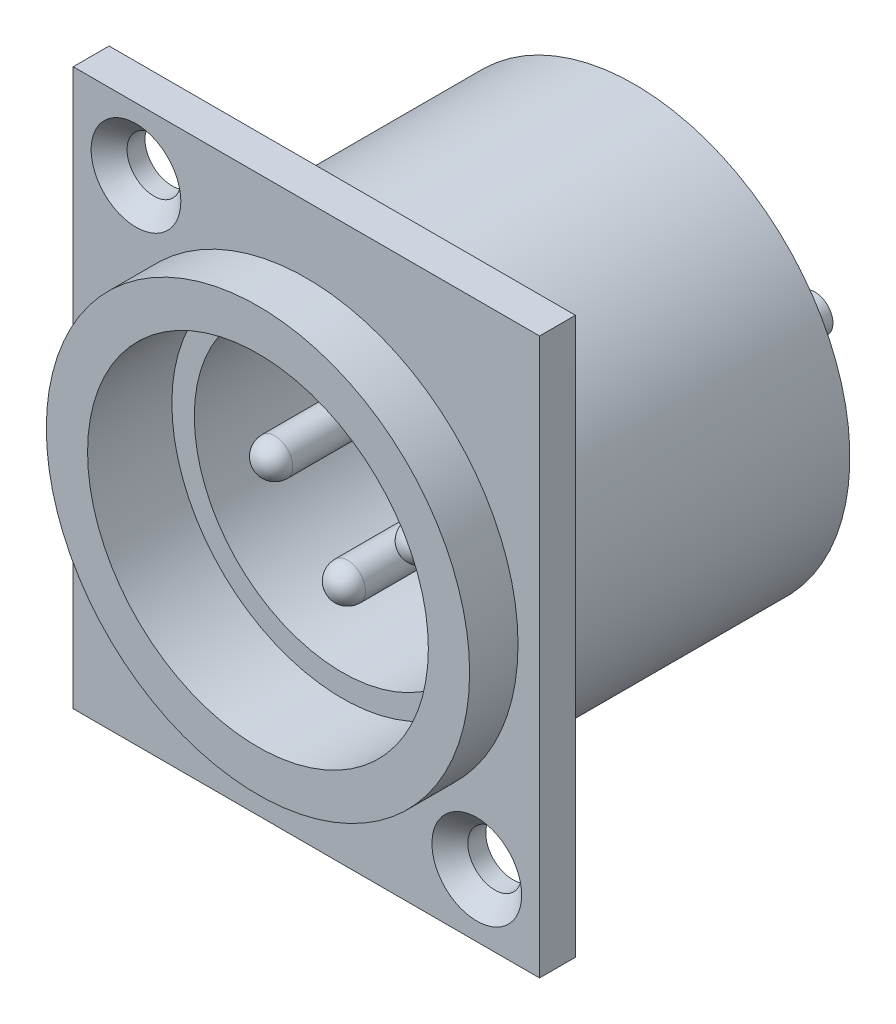
SolidWorks part; units mm, degrees
ref_plane "Plan de face" through (0, 0, 0) normal (0, 0, 1) x (1, 0, 0)
ref_plane "Plan de dessus" through (0, 0, 0) normal (0, 1, 0) x (1, 0, 0)
ref_plane "Plan de droite" through (0, 0, 0) normal (1, 0, 0) x (0, 0, -1)
sketch "Esquisse1" plane through (0, 0, 0) normal (0, 0, 1) x (1, 0, 0)
  line L1 (-9.8165, 7.8333) -> (16.1835, 7.8333)
  line L2 (-9.8165, 7.8333) -> (-9.8165, -23.1667)
  line L3 (-9.8165, -23.1667) -> (16.1835, -23.1667)
  line L4 (16.1835, 7.8333) -> (16.1835, -23.1667)
  circle A0 centre (3.1835, -7.6667) radius 9.5
  circle A1 centre (-6.3165, 4.3333) radius 1.5
  circle A2 centre (12.6835, -19.6667) radius 1.5
  dimension "D9" = 3
  dimension "D10" = 3
  dimension "D11" = 19
  dimension "D1" = 26
  dimension "D2" = 31
  dimension "D3" = 15.5
  dimension "D4" = 13
  dimension "D5" = 9.5
  dimension "D6" = 9.5
  dimension "D7" = 12
  dimension "D8" = 12
extrude "Boss.-Extru.1" add sketch "Esquisse1" along normal blind 2
sketch "Esquisse2" plane through (0, 0, 2) normal (0, 0, 1) x (1, 0, 0)
  circle A0 centre (3.1835, -7.6667) radius 9.5
  circle A1 centre (3.1835, -7.6667) radius 11.8
  dimension "D1" = 23.6
  dimension "D2" = 19
extrude "Boss.-Extru.2" add sketch "Esquisse2" along normal blind 2.7
chamfer "Chanfrein1" distance 1 angle 45 2 edges at (-4.8165, 4.3333, 2) (14.1835, -19.6667, 2)
sketch "Esquisse3" plane through (0, 0, 0) normal (0, 0, -1) x (-1, 0, 0)
  circle A0 centre (-3.1835, -7.6667) radius 8.25
  circle A1 centre (-3.1835, -7.6667) radius 12
  dimension "D1" = 16.5
  dimension "D2" = 24
extrude "Boss.-Extru.3" add sketch "Esquisse3" along normal blind 14.3
sketch "Esquisse4" plane through (0, 0, -14.3) normal (0, 0, -1) x (-1, 0, 0)
  circle A0 centre (-3.1835, -7.6667) radius 12
extrude "Boss.-Extru.4" add sketch "Esquisse4" along normal blind 2
sketch "Esquisse5" plane through (0, 0, -14.3) normal (0, 0, 1) x (1, 0, 0)
  line L0 (-4.0571, -7.6667) -> (10.2518, -7.6667) construction
  line L1 (16.1835, 7.8333) -> (-9.8165, 7.8333) construction
  line L2 (-9.8165, 7.8333) -> (-9.8165, -23.1667) construction
  circle A0 centre (7.2435, -7.6667) radius 1
  circle A1 centre (-0.8765, -7.6667) radius 1
  circle A2 centre (3.1835, -11.6467) radius 1
  dimension "D6" = 2
  dimension "D1" = 15.5
  dimension "D2" = 13
  dimension "D3" = 4.06
  dimension "D4" = 4.06
  dimension "D5" = 3.98
extrude "Boss.-Extru.5" add sketch "Esquisse5" along normal blind 15 and the other way blind 8
fillet "Congé1" radius 1 3 edges at (4.1835, -11.6467, 0.7) (8.2435, -7.6667, 0.7) (0.1235, -7.6667, 0.7)
